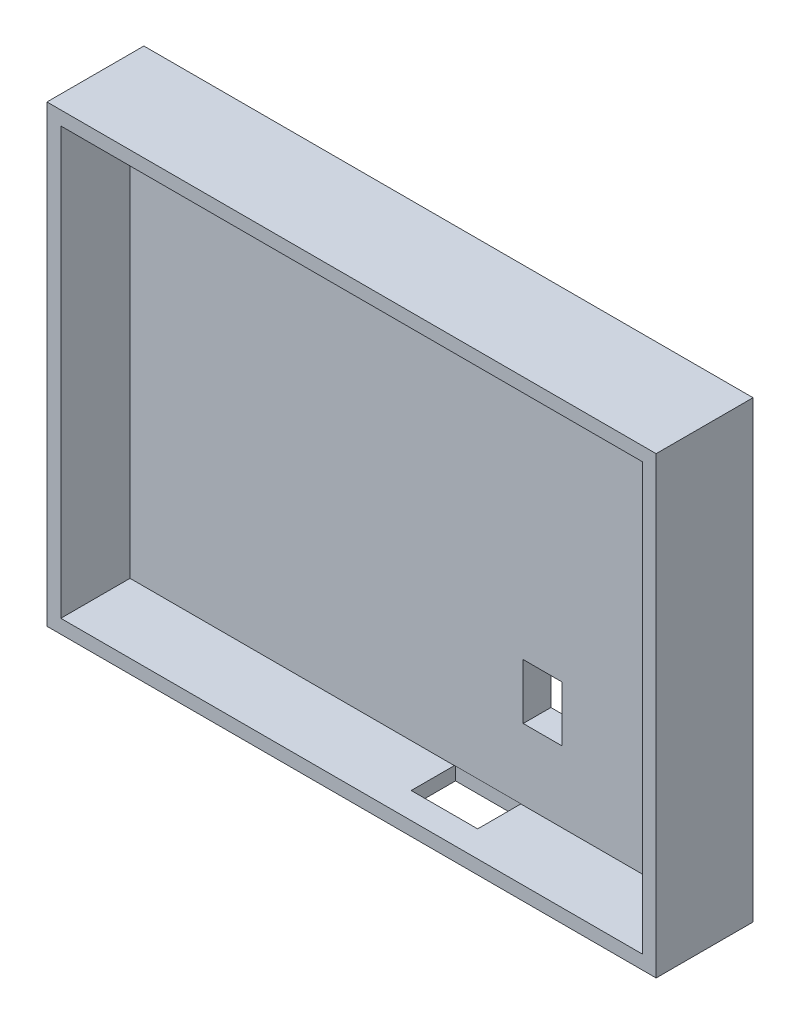
SolidWorks part; units mm, degrees
ref_plane "Front Plane" through (0, 0, 0) normal (0, 0, 1) x (1, 0, 0)
ref_plane "Top Plane" through (0, 0, 0) normal (0, 1, 0) x (1, 0, 0)
ref_plane "Right Plane" through (0, 0, 0) normal (1, 0, 0) x (0, 0, -1)
sketch "Sketch1" plane through (0, 0, 0) normal (0, 0, 1) x (1, 0, 0)
  line L1 (-55, 41) -> (55, 41)
  line L2 (-55, 41) -> (-55, -41)
  line L3 (-55, -41) -> (55, -41)
  line L4 (55, 41) -> (55, -41)
  line L5 (-55, 41) -> (55, -41) construction
  line L6 (-55, -41) -> (55, 41) construction
  point P0 (0, 0)
  dimension "D1" = 110
  dimension "D2" = 82
extrude "Boss-Extrude1" add sketch "Sketch1" along normal blind 5 contours L1 L4 L3 L2
sketch "Sketch3" plane through (0, 0, 5) normal (0, 0, 1) x (1, 0, 0)
  line L0 (-55, 41) -> (55, 41)
  line L1 (55, 41) -> (55, 38.5)
  line L2 (55, 41) -> (55, -41) construction
  line L3 (55, 38.5) -> (-55, 38.5)
  line L4 (-55, 41) -> (-55, -41) construction
  line L5 (-55, 38.5) -> (-55, 41)
  dimension "D1" = 2.5
extrude "Boss-Extrude2" add sketch "Sketch3" along normal blind 12.5
sketch "Sketch4" plane through (0, 0, 5) normal (0, 0, 1) x (1, 0, 0)
  line L0 (-55, 38.5) -> (-55, -41)
  line L1 (-55, -41) -> (-52.5, -41)
  line L2 (-55, -41) -> (55, -41) construction
  line L3 (-52.5, -41) -> (-52.5, 38.5)
  line L4 (-55, 38.5) -> (55, 38.5) construction
  line L5 (-52.5, 38.5) -> (-55, 38.5)
  dimension "D1" = 2.5
extrude "Boss-Extrude3" add sketch "Sketch4" along normal blind 12.5 contours L5 L0 L1 L3
sketch "Sketch5" plane through (0, 0, 5) normal (0, 0, 1) x (1, 0, 0)
  line L0 (-52.5, -41) -> (55, -41)
  line L1 (55, -41) -> (55, -38.5)
  line L2 (55, 38.5) -> (55, -41) construction
  line L3 (55, -38.5) -> (-52.5, -38.5)
  line L4 (-52.5, -41) -> (-52.5, 38.5) construction
  line L5 (-52.5, -38.5) -> (-52.5, -41)
  dimension "D1" = 2.5
extrude "Boss-Extrude4" add sketch "Sketch5" along normal blind 12.5
sketch "Sketch6" plane through (0, 0, 5) normal (0, 0, 1) x (1, 0, 0)
  line L0 (55, 38.5) -> (55, -38.5)
  line L1 (55, -38.5) -> (52.5, -38.5)
  line L2 (55, -38.5) -> (-52.5, -38.5) construction
  line L3 (52.5, -38.5) -> (52.5, 38.5)
  line L4 (-52.5, 38.5) -> (55, 38.5) construction
  line L5 (52.5, 38.5) -> (55, 38.5)
  dimension "D1" = 2.5
extrude "Boss-Extrude5" add sketch "Sketch6" along normal blind 12.5
sketch "Sketch7" plane through (0, 0, 5) normal (0, 0, 1) x (1, 0, 0)
  line L0 (25.5, -38.5) -> (25.5, -25.7)
  line L1 (52.5, -38.5) -> (-52.5, -38.5) construction
  line L2 (52.5, -25.7) -> (25.5, -25.7)
  line L3 (52.5, 38.5) -> (52.5, -38.5) construction
  line L4 (25.5, -25.7) -> (18.5, -25.7)
  line L5 (18.5, -25.7) -> (18.5, -15.7)
  line L6 (18.5, -15.7) -> (25.5, -15.7)
  line L7 (25.5, -15.7) -> (25.5, -25.7)
  dimension "D1" = 12.8
  dimension "D2" = 27
  dimension "D3" = 7
  dimension "D4" = 10
extrude "Cut-Extrude1" cut sketch "Sketch7" against normal blind 12.5 contours L4 L5 L6 L7
sketch "Sketch8" plane through (0, -41, 0) normal (0, -1, 0) x (1, 0, 0)
  line L2 (18.0659, 4.7924) -> (6.0659, 4.7924)
  line L3 (6.0659, 4.7924) -> (6.0659, 12.7924)
  line L4 (6.0659, 12.7924) -> (18.0659, 12.7924)
  line L5 (18.0659, 12.7924) -> (18.0659, 4.7924)
  point P0 (0, 0)
extrude "Cut-Extrude2" cut sketch "Sketch8" against normal blind 2.54 contours L2 L3 L4 L5
